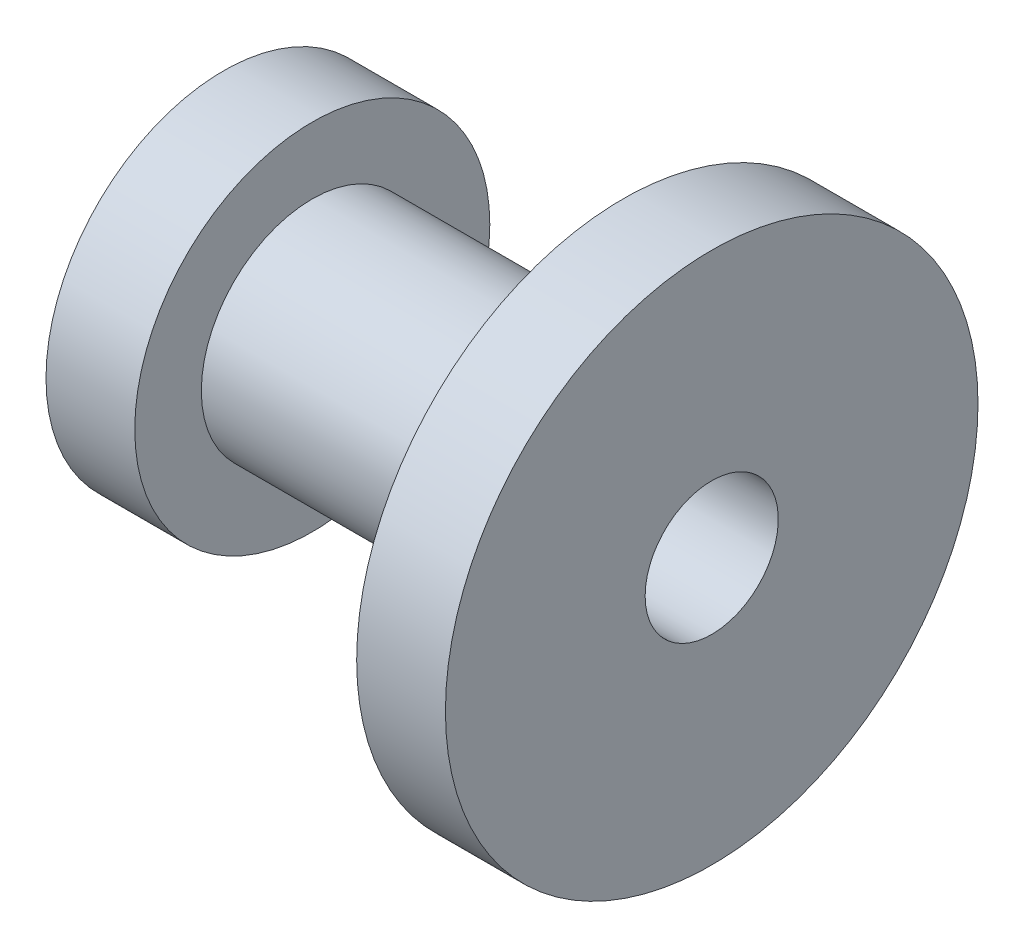
SolidWorks part; units mm, degrees
ref_plane "정면" through (0, 0, 0) normal (0, 0, 1) x (1, 0, 0)
ref_plane "윗면" through (0, 0, 0) normal (0, 1, 0) x (1, 0, 0)
ref_plane "우측면" through (0, 0, 0) normal (1, 0, 0) x (0, 0, -1)
sketch "스케치2" plane through (0, 0, 0) normal (0, 0, 1) x (1, 0, 0)
  line L0 (0, 0) -> (0, 40)
  line L1 (0, 40) -> (20, 40)
  line L2 (20, 40) -> (20, 25)
  line L3 (20, 25) -> (90, 25)
  line L4 (90, 25) -> (90, 60)
  line L5 (90, 60) -> (110, 60)
  line L6 (110, 60) -> (110, 0)
  line L7 (0, 0) -> (110, 0) construction
  line L8 (0, 0) -> (110, 0)
  dimension "D1" = 80
  dimension "D2" = 120
  dimension "D3" = 20
  dimension "D4" = 20
  dimension "D5" = 110
  dimension "D6" = 50
revolve "회전1" add sketch "스케치2" angle 360 about L7
sketch "스케치3" plane through (0, 0, 0) normal (-1, 0, 0) x (0, 0, 1)
  circle A0 centre (0, 0) radius 15
  dimension "D1" = 30
extrude "컷-돌출1" cut sketch "스케치3" against normal blind 227
